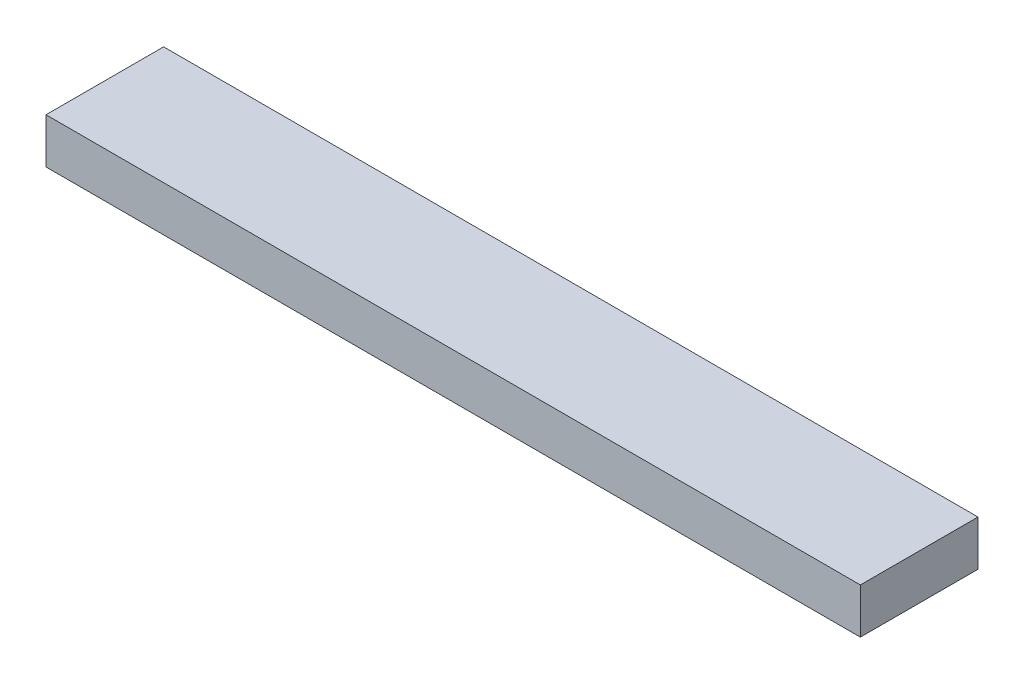
SolidWorks part; units mm, degrees
ref_plane "Front Plane" through (0, 0, 0) normal (0, 0, 1) x (1, 0, 0)
ref_plane "Top Plane" through (0, 0, 0) normal (0, 1, 0) x (1, 0, 0)
ref_plane "Right Plane" through (0, 0, 0) normal (1, 0, 0) x (0, 0, -1)
sketch "Sketch1" plane through (0, 0, 0) normal (0, 1, 0) x (1, 0, 0)
  line L1 (-57.15, -8.255) -> (57.15, -8.255)
  line L2 (-57.15, -8.255) -> (-57.15, 8.255)
  line L3 (-57.15, 8.255) -> (57.15, 8.255)
  line L4 (57.15, -8.255) -> (57.15, 8.255)
  line L5 (-57.15, -8.255) -> (57.15, 8.255) construction
  line L6 (-57.15, 8.255) -> (57.15, -8.255) construction
  point P0 (0, 0)
  dimension "D1" = 114.3
  dimension "D2" = 16.51
extrude "Boss-Extrude1" add sketch "Sketch1" along normal blind 6.35
